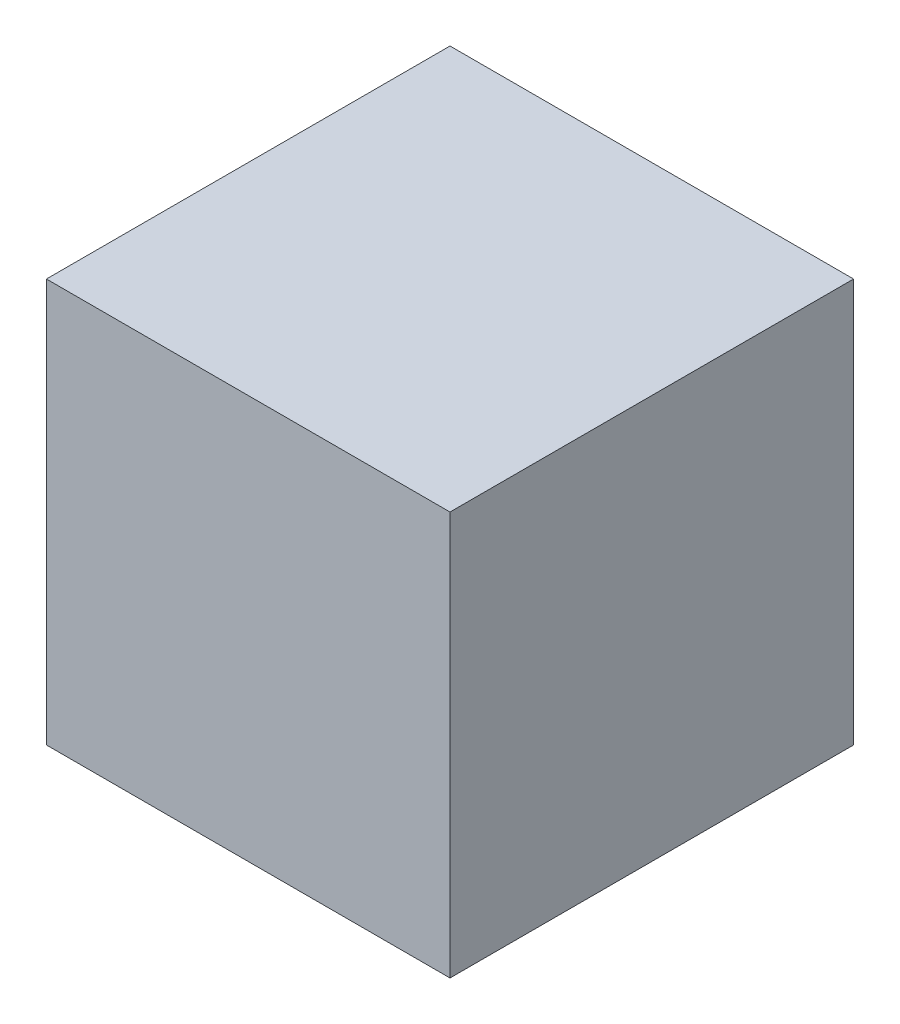
SolidWorks part; units mm, degrees
ref_plane "Ebene vorne" through (0, 0, 0) normal (0, 0, 1) x (1, 0, 0)
ref_plane "Ebene oben" through (0, 0, 0) normal (0, 1, 0) x (1, 0, 0)
ref_plane "Ebene rechts" through (0, 0, 0) normal (1, 0, 0) x (0, 0, -1)
sketch "Skizze1" plane through (0, 0, 0) normal (0, 0, 1) x (1, 0, 0)
  line L1 (0, 0) -> (50, 0)
  line L2 (0, 0) -> (0, 50)
  line L3 (0, 50) -> (50, 50)
  line L4 (50, 0) -> (50, 50)
  dimension "D1" = 50
  dimension "D2" = 50
extrude "Aufsatz-Linear austragen1" add sketch "Skizze1" along normal blind 50
